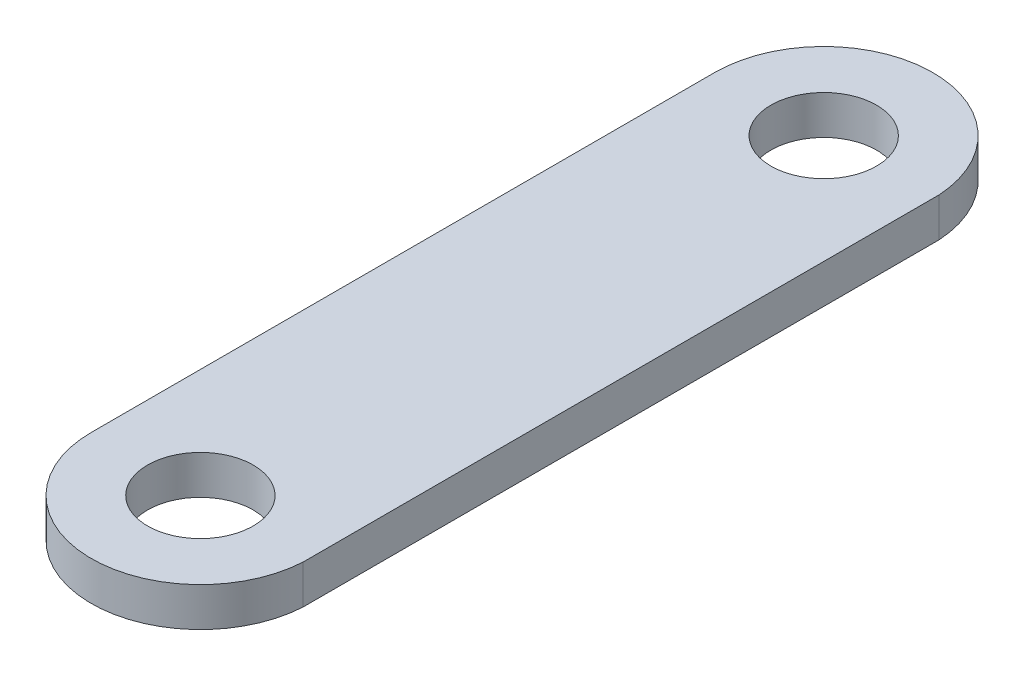
SolidWorks part; units mm, degrees
material "6061-T6 (SS)"
ref_plane "Front Plane" through (0, 0, 0) normal (0, 0, 1) x (1, 0, 0)
ref_plane "Top Plane" through (0, 0, 0) normal (0, 1, 0) x (1, 0, 0)
ref_plane "Right Plane" through (0, 0, 0) normal (1, 0, 0) x (0, 0, -1)
sketch "Sketch1" plane through (0, 0, 0) normal (0, 1, 0) x (1, 0, 0)
  line L0 (-4.445, 0) -> (4.445, 0) construction
  line L3 (-4.445, 12.7) -> (-4.445, -12.7)
  line L4 (4.445, 12.9639) -> (4.445, -12.9639)
  arc A0 (-4.445, 12.7) -> (4.445, 12.9639) centre (0.0039, 12.7) cw
  circle A2 centre (0.0039, 12.7) radius 2.1526
  circle A3 centre (0.0039, -12.7) radius 2.1526
  arc A4 (-4.445, -12.7) -> (4.445, -12.9639) centre (0.0039, -12.7) ccw
  point P4 (0, 0)
  point P7 (-4.445, 0)
  point P10 (4.445, 0)
  dimension "D3" = 4.3053
  dimension "D1" = 8.89
  dimension "D2" = 12.7
extrude "Boss-Extrude1" add sketch "Sketch1" along normal blind 1.5875
